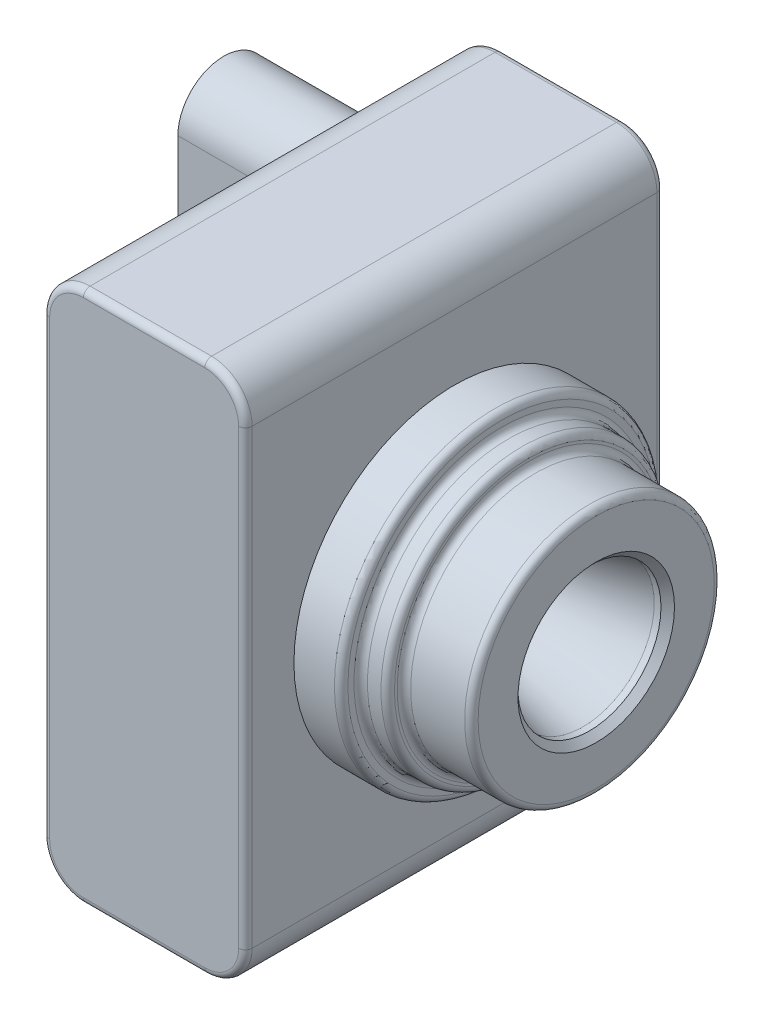
SolidWorks part; units mm, degrees
ref_plane "Front Plane" through (0, 0, 0) normal (0, 0, 1) x (1, 0, 0)
ref_plane "Top Plane" through (0, 0, 0) normal (0, 1, 0) x (1, 0, 0)
ref_plane "Right Plane" through (0, 0, 0) normal (1, 0, 0) x (0, 0, -1)
sketch "Sketch1" plane through (0, 0, 0) normal (0, 0, 1) x (1, 0, 0)
  line L1 (-4.5, -19.75) -> (4.5, -19.75)
  line L2 (-7.5, -16.75) -> (-7.5, 16.75)
  line L3 (-4.5, 19.75) -> (4.5, 19.75)
  line L4 (7.5, -16.75) -> (7.5, 16.75)
  line L5 (-7.5, -19.75) -> (7.5, 19.75) construction
  line L6 (-7.5, 19.75) -> (7.5, -19.75) construction
  arc A0 (4.5, -19.75) -> (7.5, -16.75) centre (4.5, -16.75) ccw
  arc A1 (-4.5, -19.75) -> (-7.5, -16.75) centre (-4.5, -16.75) cw
  arc A2 (4.5, 19.75) -> (7.5, 16.75) centre (4.5, 16.75) cw
  arc A3 (-7.5, 16.75) -> (-4.5, 19.75) centre (-4.5, 16.75) cw
  point P0 (0, 0)
  dimension "D3" = 3
  dimension "D1" = 39.5
  dimension "D2" = 15
extrude "Boss-Extrude1" add sketch "Sketch1" along normal blind 31
sketch "Sketch2" plane through (7.5, 0, 0) normal (1, 0, 0) x (0, 0, -1)
  line L0 (-15.5, -16.75) -> (-15.5, 0) construction
  line L1 (-31, -16.75) -> (0, -16.75) construction
  line L2 (-15.5, 0) -> (0, 0) construction
  circle A0 centre (-15.5, 0) radius 11.9
  dimension "D1" = 23.8
extrude "Boss-Extrude2" add sketch "Sketch2" along normal blind 3.5
sketch "Sketch3" plane through (11, 0, 0) normal (1, 0, 0) x (0, 0, -1)
  circle A0 centre (-15.5, 0) radius 10.45
  dimension "D1" = 20.9
extrude "Boss-Extrude3" add sketch "Sketch3" along normal blind 2
sketch "Sketch4" plane through (13, 0, 0) normal (1, 0, 0) x (0, 0, -1)
  circle A0 centre (-15.5, 0) radius 9.25
  dimension "D1" = 18.5
extrude "Boss-Extrude4" add sketch "Sketch4" along normal blind 5
sketch "Sketch5" plane through (18, 0, 0) normal (1, 0, 0) x (0, 0, -1)
  circle A0 centre (-15.5, 0) radius 5.3
  dimension "D1" = 10.6
extrude "Cut-Extrude1" cut sketch "Sketch5" against normal blind 17
fillet "Fillet2" radius 0.5 2 edges at (13, 0, 6.25) (11, 0, 5.05)
fillet "Fillet3" radius 0.5 3 edges at (18, 0, 6.25) (13, 0, 5.05) (11, 0, 3.6)
chamfer "Chamfer1" distance 0.5 angle 45 1 edges at (18, 0, 10.2)
sketch "Sketch6" plane through (1, 0, 0) normal (1, 0, 0) x (0, 0, -1)
  circle A0 centre (-15.5, 0) radius 1.1542
extrude "Cut-Extrude2" cut sketch "Sketch6" against normal blind 2
chamfer "Chamfer4" distance 16 angle 14 1 edges at (1, 0, 10.2)
sketch "Sketch7" plane through (-7.5, 0, 0) normal (-1, 0, 0) x (0, 0, 1)
  line L0 (0, 16.75) -> (0, -16.75) construction
  line L1 (31, 19.75) -> (0, 19.75) construction
  line L2 (11, 13.15) -> (11, -11.85)
  line L3 (11, -11.85) -> (4.2, -11.85)
  line L4 (4.2, -11.85) -> (4.2, 13.15)
  arc A0 (11, 13.15) -> (4.2, 13.15) centre (7.6, 13.15) ccw
  dimension "D1" = 7.6
  dimension "D2" = 6.6
  dimension "D3" = 6.8
  dimension "D4" = 25
extrude "Boss-Extrude5" add sketch "Sketch7" along normal blind 10
fillet "Fillet4" radius 0.5 16 edges at (-6.6213, 18.8713, 0) (0, 19.75, 0) (6.6213, 18.8713, 0) (7.5, 0, 0) (6.6213, -18.8713, 0) (0, -19.75, 0) (-6.6213, -18.8713, 0) (-6.6213, 18.8713, 31) (0, 19.75, 31) (6.6213, 18.8713, 31) (7.5, 0, 31) (6.6213, -18.8713, 31) (0, -19.75, 31) (-6.6213, -18.8713, 31) (-7.5, 0, 0) (-7.5, 0, 31)
